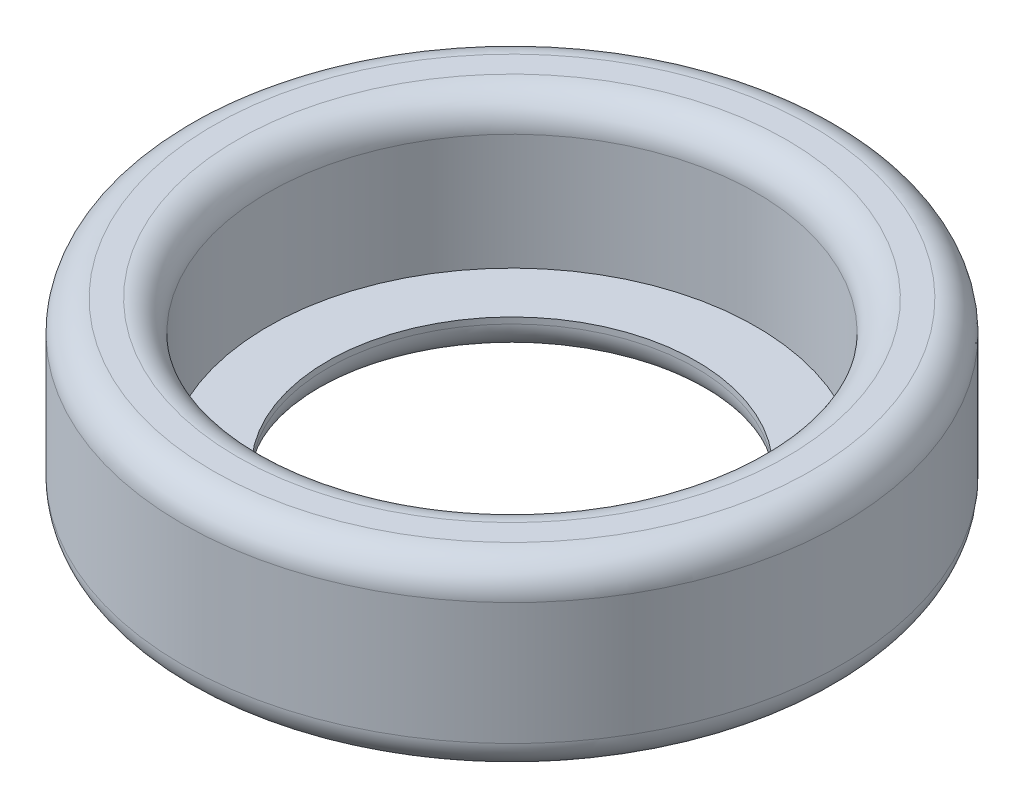
SolidWorks part; units mm, degrees
material "PA Type 6"
ref_plane "Plan de face" through (0, 0, 0) normal (0, 0, 1) x (1, 0, 0)
ref_plane "Plan de dessus" through (0, 0, 0) normal (0, 1, 0) x (1, 0, 0)
ref_plane "Plan de droite" through (0, 0, 0) normal (1, 0, 0) x (0, 0, -1)
sketch "Esquisse1" plane through (0, 0, 0) normal (0, 1, 0) x (1, 0, 0)
  circle A0 centre (0, 0) radius 27
  circle A1 centre (0, 0) radius 15.1
extrude "Boss.-Extru.1" add sketch "Esquisse1" along normal blind 15
sketch "Esquisse2" plane through (0, 15, 0) normal (0, 1, 0) x (-1, 0, 0)
  circle A0 centre (0, 0) radius 20
extrude "Enlèv. mat.-Extru.1" cut sketch "Esquisse2" against normal blind 12
fillet "Congé1" radius 2.5 4 edges at (0, 0, 15.1) (0, 0, 27) (0, 15, 27) (0, 15, 20)
